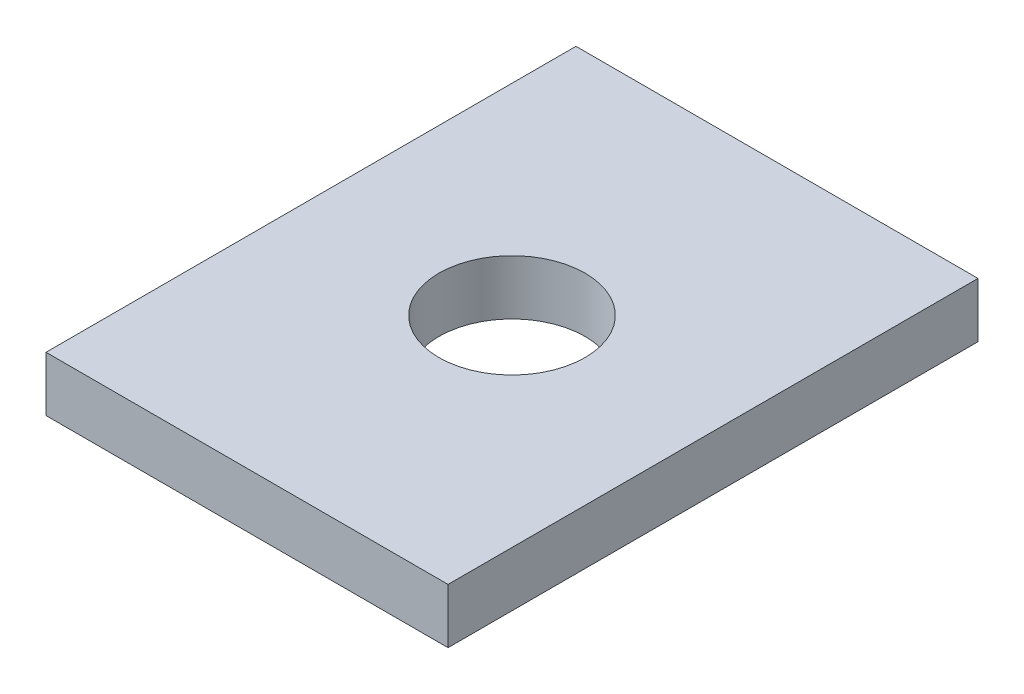
SolidWorks part; units mm, degrees
material "Oak"
ref_plane "Front Plane" through (0, 0, 0) normal (0, 0, 1) x (1, 0, 0)
ref_plane "Top Plane" through (0, 0, 0) normal (0, 1, 0) x (1, 0, 0)
ref_plane "Right Plane" through (0, 0, 0) normal (1, 0, 0) x (0, 0, -1)
sketch "Sketch1" plane through (0, 0, 0) normal (0, 1, 0) x (1, 0, 0)
  line L1 (-69.85, -92.075) -> (69.85, -92.075)
  line L2 (-69.85, -92.075) -> (-69.85, 92.075)
  line L3 (-69.85, 92.075) -> (69.85, 92.075)
  line L4 (69.85, -92.075) -> (69.85, 92.075)
  line L5 (-69.85, -92.075) -> (69.85, 92.075) construction
  line L6 (-69.85, 92.075) -> (69.85, -92.075) construction
  circle A0 centre (0, 0) radius 25.4
  point P0 (0, 0)
  dimension "D3" = 50.8
  dimension "D1" = 139.7
  dimension "6.75" = 184.15
extrude "Boss-Extrude1" add sketch "Sketch1" along normal blind 19.05
